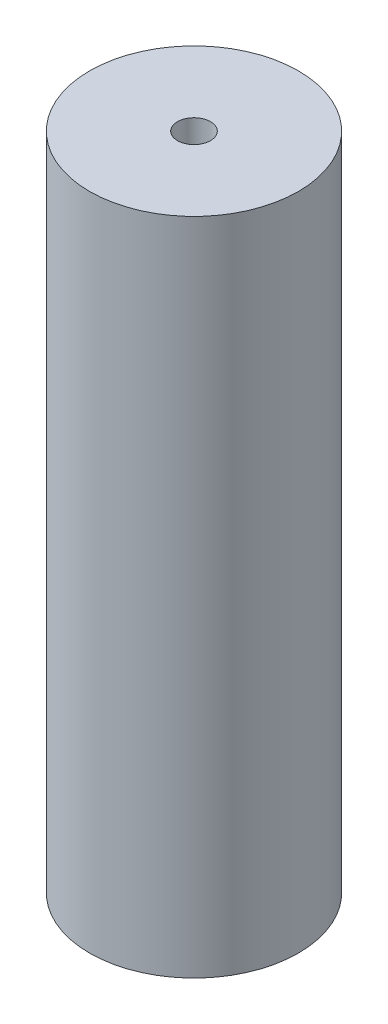
SolidWorks part; units mm, degrees
ref_plane "Front Plane" through (0, 0, 0) normal (0, 0, 1) x (1, 0, 0)
ref_plane "Top Plane" through (0, 0, 0) normal (0, 1, 0) x (1, 0, 0)
ref_plane "Right Plane" through (0, 0, 0) normal (1, 0, 0) x (0, 0, -1)
sketch "Sketch2" plane through (0, 0, 0) normal (0, 1, 0) x (1, 0, 0)
  circle A0 centre (0, 0) radius 9.5
  dimension "D1" = 19
extrude "Boss-Extrude1" add sketch "Sketch2" along normal mid plane 60
sketch "Sketch3" plane through (0, 30, 0) normal (0, 1, 0) x (1, 0, 0)
  circle A0 centre (0, 0) radius 1.5
  dimension "D1" = 3
extrude "Cut-Extrude1" cut sketch "Sketch3" against normal through all
equation "\"6ö\"=10"
